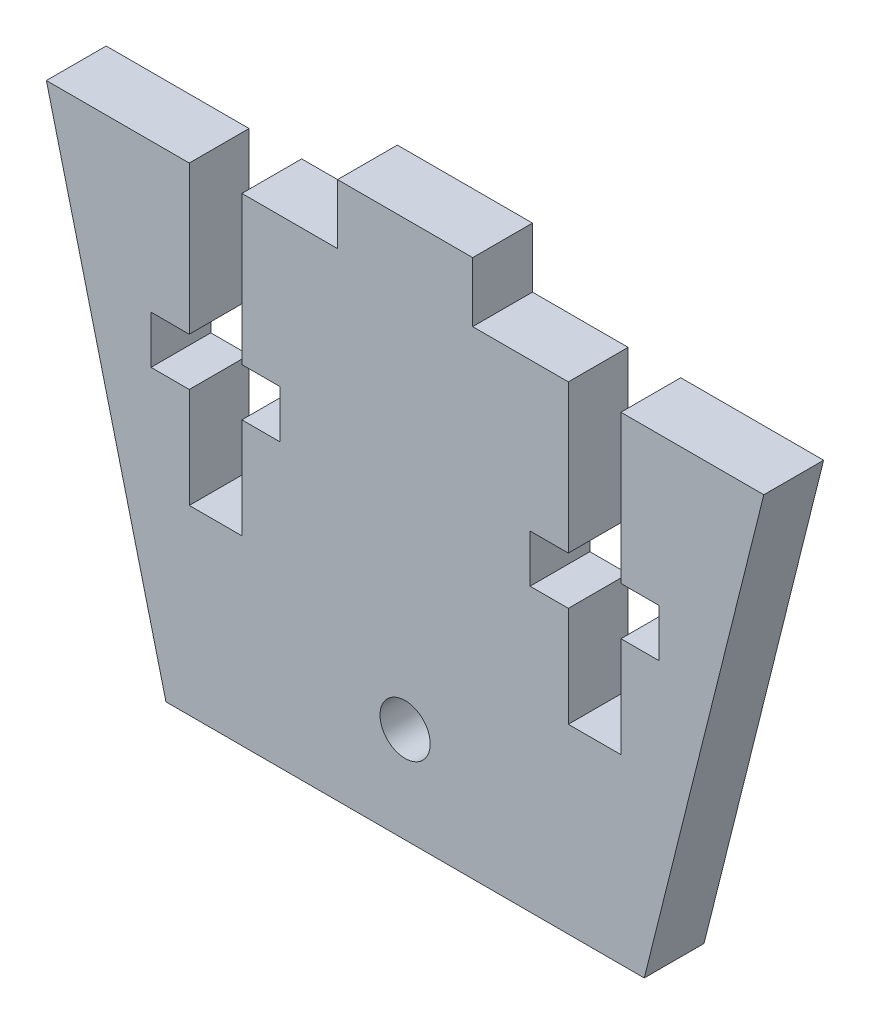
SolidWorks part; units mm, degrees
ref_plane "Front Plane" through (0, 0, 0) normal (0, 0, 1) x (1, 0, 0)
ref_plane "Top Plane" through (0, 0, 0) normal (0, 1, 0) x (1, 0, 0)
ref_plane "Right Plane" through (0, 0, 0) normal (1, 0, 0) x (0, 0, -1)
sketch "Sketch1" plane through (0, 0, 0) normal (0, 0, 1) x (1, 0, 0)
  line L0 (0, 0) -> (0, 25.4)
  line L1 (-19.05, 25.4) -> (-12.7, 0)
  line L2 (19.05, 25.4) -> (12.7, 0)
  line L3 (-3.5877, 25.4) -> (-3.5877, 28.575)
  line L4 (-3.5877, 25.4) -> (3.5877, 25.4)
  line L5 (-19.05, 25.4) -> (19.05, 25.4)
  line L6 (-12.7, 0) -> (12.7, 0)
  line L7 (0, 25.4) -> (0, 28.575)
  line L8 (-3.5877, 28.575) -> (3.5877, 28.575)
  line L9 (3.5877, 25.4) -> (3.5877, 28.575)
  line L10 (-10.0647, 9.652) -> (-10.0647, 25.4)
  line L11 (-11.4618, 25.4) -> (-8.6677, 25.4)
  line L12 (-11.4618, 25.4) -> (-11.4617, 9.652)
  line L13 (-11.4617, 9.652) -> (-8.6677, 9.652)
  line L14 (-8.6677, 25.4) -> (-8.6677, 9.652)
  line L15 (-13.4937, 17.526) -> (-6.6358, 17.526)
  line L16 (-6.6358, 17.526) -> (-6.6357, 14.986)
  line L17 (-6.6357, 14.986) -> (-13.4937, 14.986)
  line L18 (-13.4937, 17.526) -> (-13.4937, 14.986)
  line L19 (13.4937, 17.526) -> (13.4937, 14.986)
  line L20 (6.6357, 14.986) -> (13.4937, 14.986)
  line L21 (13.4937, 17.526) -> (6.6358, 17.526)
  line L22 (6.6358, 17.526) -> (6.6357, 14.986)
  line L23 (11.4617, 9.652) -> (8.6677, 9.652)
  line L24 (8.6677, 25.4) -> (8.6677, 9.652)
  line L25 (11.4618, 25.4) -> (11.4617, 9.652)
  circle A0 centre (0, 5.08) radius 1.3335
  point P12 (0, 5.08)
  point P26 (-10.0647, 14.986)
  point P27 (-10.0647, 17.526)
  dimension "D6" = 2.667
  dimension "D1" = 25.4
  dimension "D2" = 38.1
  dimension "D3" = 3.175
  dimension "D4" = 3.5877
  dimension "D5" = 5.08
  dimension "D7" = 5.08
  dimension "D8" = 2.794
  dimension "D9" = 15.748
  dimension "D10" = 3.429
  dimension "D11" = 2.54
  dimension "D12" = 25.4
  dimension "D13" = 5.08
extrude "Boss-Extrude1" add sketch "Sketch1" along normal blind 3.175 contours A0 L0 L6 L2 L5 L25 L21 L19 L20 L23 L24 L22 L4 | A0 L0 L4 L5 L14 L15 L16 L17 L13 L12 L18 L1 L6 | L4 L9 L8 L7 | L8 L3 L4 L7
